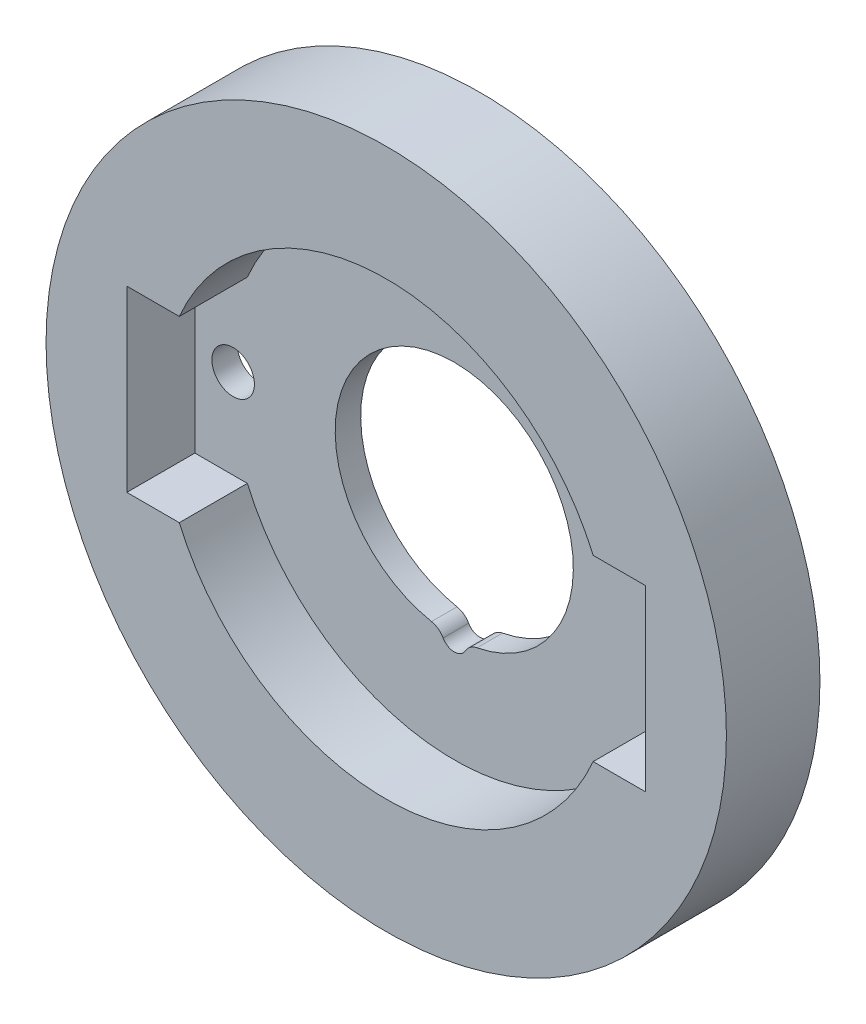
SolidWorks part; units mm, degrees
ref_plane "Ebene vorne" through (0, 0, 0) normal (0, 0, 1) x (1, 0, 0)
ref_plane "Ebene oben" through (0, 0, 0) normal (0, 1, 0) x (1, 0, 0)
ref_plane "Ebene rechts" through (0, 0, 0) normal (1, 0, 0) x (0, 0, -1)
sketch "Skizze1" plane through (0, 0, 0) normal (0, 0, 1) x (1, 0, 0)
  circle A0 centre (0, 0) radius 20
  circle A1 centre (0, 0) radius 7
  dimension "D1" = 40
  dimension "D2" = 14
extrude "Aufsatz-Linear austragen1" add sketch "Skizze1" along normal blind 5.5
sketch "Skizze2" plane through (0, 0, 5.5) normal (0, 0, 1) x (1, 0, 0)
  line L1 (-15.25, -5.25) -> (15.25, -5.25)
  line L2 (-15.25, -5.25) -> (-15.25, 5.25)
  line L3 (-15.25, 5.25) -> (15.25, 5.25)
  line L4 (15.25, -5.25) -> (15.25, 5.25)
  line L5 (-15.25, -5.25) -> (15.25, 5.25) construction
  line L6 (-15.25, 5.25) -> (15.25, -5.25) construction
  circle A0 centre (0, 0) radius 13.25
  circle M2 centre (0, 0) radius 7
  dimension "D1" = 26.5
  dimension "D2" = 10.5
  dimension "D3" = 30.5
extrude "Schnitt-Linear austragen1" cut sketch "Skizze2" against normal blind 4 contours L1 A0 M2 | L3 A0 L1 M2 | L1 A0 L3 M2 | L3 A0 M2 | A0 L3 L2 L1 | A0 L1 L4 L3
sketch "Skizze3" plane through (0, 0, 5.5) normal (0, 0, 1) x (1, 0, 0)
  line L0 (0, 13.25) -> (0, -13.25) construction
  arc A0 (12.1655, 5.25) -> (-12.1655, 5.25) centre (0, 0) ccw construction
  arc A1 (-12.1655, -5.25) -> (12.1655, -5.25) centre (0, 0) ccw construction
  circle A2 centre (13, 0) radius 1.25
  circle A3 centre (-13, 0) radius 1.25
  dimension "D2" = 2.5
  dimension "D1" = 13
extrude "Schnitt-Linear austragen2" cut sketch "Skizze3" against normal up to next contours A3 | A2
sketch "Skizze4" plane through (0, 0, 1.5) normal (0, 0, 1) x (1, 0, 0)
  circle A0 centre (0, -7) radius 0.75
  dimension "D1" = 1.5
  dimension "D2" = 7
extrude "Schnitt-Linear austragen3" cut sketch "Skizze4" against normal up to next contours A0
fillet "Verrundung1" radius 1 2 edges at (-0.7489, -6.9598, 0.75) (0.7489, -6.9598, 0.75)
